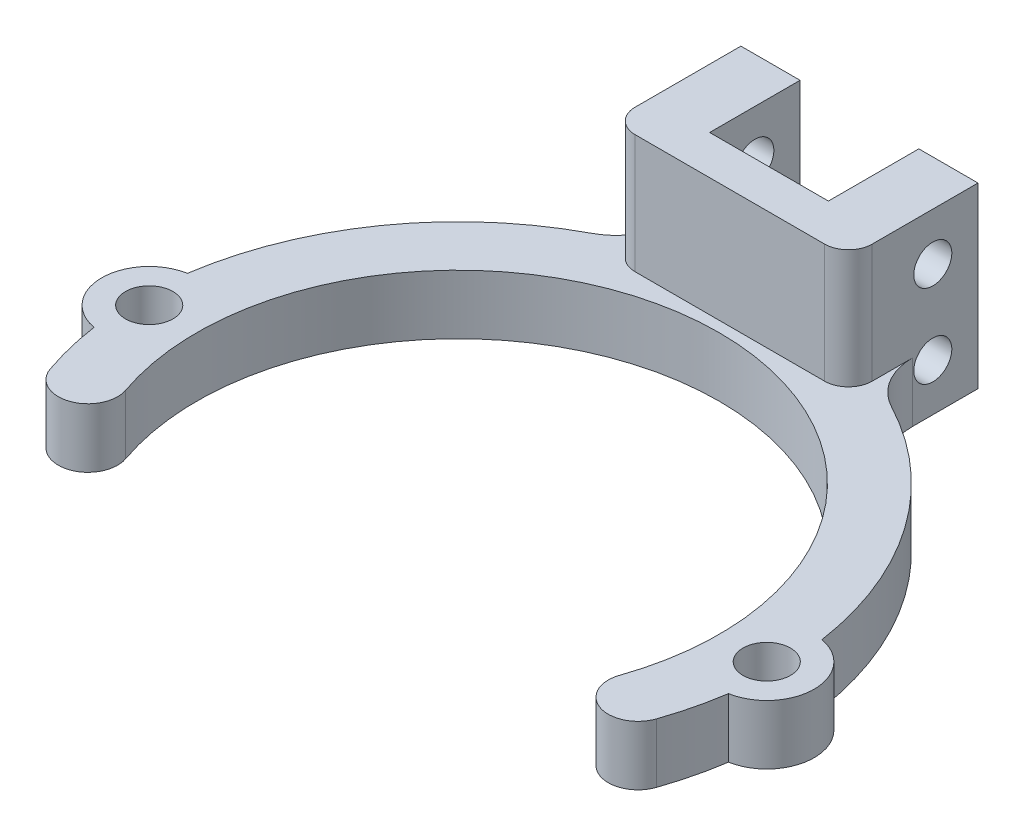
SolidWorks part; units mm, degrees
ref_plane "前视基准面" through (0, 0, 0) normal (0, 0, 1) x (1, 0, 0)
ref_plane "上视基准面" through (0, 0, 0) normal (0, 1, 0) x (1, 0, 0)
ref_plane "右视基准面" through (0, 0, 0) normal (1, 0, 0) x (0, 0, -1)
sketch "草图1" plane through (0, 0, 0) normal (0, 1, 0) x (1, 0, 0)
  line L0 (-28.9941, -8) -> (32.5349, -8) construction
  line L1 (0, 0) -> (0, -8) construction
  line L2 (0, 22) -> (0, 27) construction
  line L3 (0, 0) -> (0, 22) construction
  arc A0 (20.7941, -7.1837) -> (-20.7941, -7.1837) centre (0, 0) ccw
  circle A4 centre (-26, 0) radius 2
  arc A5 (-26.7115, 3.9362) -> (-26.7115, -3.9362) centre (-26, 0) ccw
  circle A7 centre (0, 0) radius 24.5 construction
  arc A8 (26.7115, 3.9362) -> (-26.7115, 3.9362) centre (0, 0) ccw
  arc A9 (-26.7115, -3.9362) -> (-25.52, -8.8163) centre (0, 0) ccw
  arc A10 (20.7941, -7.1837) -> (25.52, -8.8163) centre (23.1571, -8) ccw
  arc A11 (-25.52, -8.8163) -> (-20.7941, -7.1837) centre (-23.1571, -8) ccw
  arc A12 (25.52, -8.8163) -> (26.7115, -3.9362) centre (0, 0) ccw
  arc A13 (26.7115, 3.9362) -> (26.7115, -3.9362) centre (26, 0) cw
  circle A14 centre (26, 0) radius 2
  point P16 (0, 24.5)
  point P18 (-23.1571, -8)
  point P19 (23.1571, -8)
extrude "凸台-拉伸1" add sketch "草图1" along normal blind 5
sketch "草图3" plane through (0, 0, 0) normal (0, 1, 0) x (1, 0, 0)
  line L0 (0, 0) -> (0, 30) construction
  line L1 (-5, 33.807) -> (-9.9829, 33.807)
  line L2 (9.9829, 22.8964) -> (-9.9829, 22.8964)
  line L3 (9.9829, 22.8964) -> (9.9829, 33.807)
  line L4 (9.9829, 33.807) -> (5, 33.807)
  line L5 (-9.9829, 22.8964) -> (-9.9829, 33.807)
  line L6 (9.9829, 22.8964) -> (-9.9829, 33.807) construction
  line L7 (9.9829, 33.807) -> (-9.9829, 22.8964) construction
  line L8 (5, 26.193) -> (-5, 26.193)
  line L9 (5, 26.193) -> (5, 33.807)
  line L10 (-5, 26.193) -> (-5, 33.807)
  line L11 (5, 26.193) -> (-5, 33.807) construction
  line L12 (5, 33.807) -> (-5, 26.193) construction
  point P6 (0, 30)
  point P7 (0, 30)
extrude "凸台-拉伸2" add sketch "草图3" along normal blind 15
sketch "草图5" plane through (0, 5, 0) normal (0, 1, 0) x (1, 0, 0)
  line L0 (9.9829, 33.807) -> (5, 33.807) construction
  line L1 (-5, 26.193) -> (5, 26.193)
  line L2 (-5, 26.193) -> (-5, 33.807)
  line L3 (-5, 33.807) -> (5, 33.807)
  line L4 (5, 26.193) -> (5, 33.807)
  line L5 (5, 33.807) -> (5, 26.193) construction
extrude "切除-拉伸2" cut sketch "草图5" against normal through all
sketch "草图4" plane through (-9.9829, 0, 0) normal (-1, 0, 0) x (0, 0, 1)
  circle A0 centre (-30, 4) radius 1.6
  circle A1 centre (-30, 11) radius 1.6
extrude "切除-拉伸1" cut sketch "草图4" against normal through all
fillet "圆角2" radius 5 2 edges at (9.9829, 2.5, -25.0867) (-9.9829, 2.5, -25.0867)
fillet "圆角3" radius 2 2 edges at (9.9829, 10, -22.8964) (-9.9829, 10, -22.8964)
